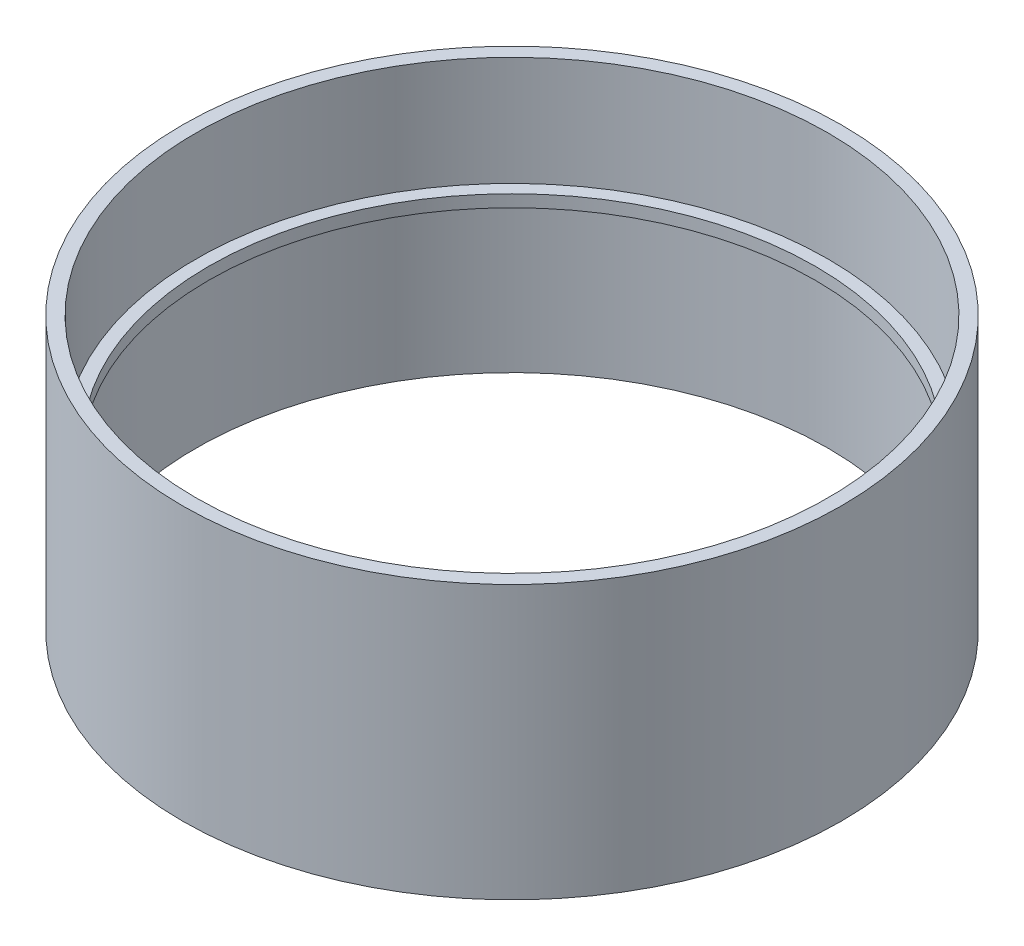
SolidWorks part; units mm, degrees
ref_plane "Front Plane" through (0, 0, 0) normal (0, 0, 1) x (1, 0, 0)
ref_plane "Top Plane" through (0, 0, 0) normal (0, 1, 0) x (1, 0, 0)
ref_plane "Right Plane" through (0, 0, 0) normal (1, 0, 0) x (0, 0, -1)
sketch "Sketch2" plane through (0, 0, 0) normal (0, 0, 1) x (1, 0, 0)
  line L0 (0, 0) -> (0, 38.3887) construction
  line L1 (39.6875, 0) -> (39.6875, 19.05)
  line L2 (39.6875, 19.05) -> (38.1, 19.05)
  line L3 (38.1, 19.05) -> (38.1, 20.574)
  line L4 (38.1, 20.574) -> (39.6875, 20.574)
  line L5 (39.6875, 20.574) -> (39.6875, 34.29)
  line L6 (39.6875, 34.29) -> (41.402, 34.29)
  line L7 (41.402, 34.29) -> (41.402, 0)
  line L8 (41.402, 0) -> (39.6875, 0)
  dimension "D1" = 1.524
  dimension "D2" = 79.375
  dimension "D3" = 82.804
  dimension "D4" = 19.05
  dimension "D5" = 34.29
  dimension "D6" = 76.2
revolve "Revolve1" add sketch "Sketch2" angle 360 about L0
